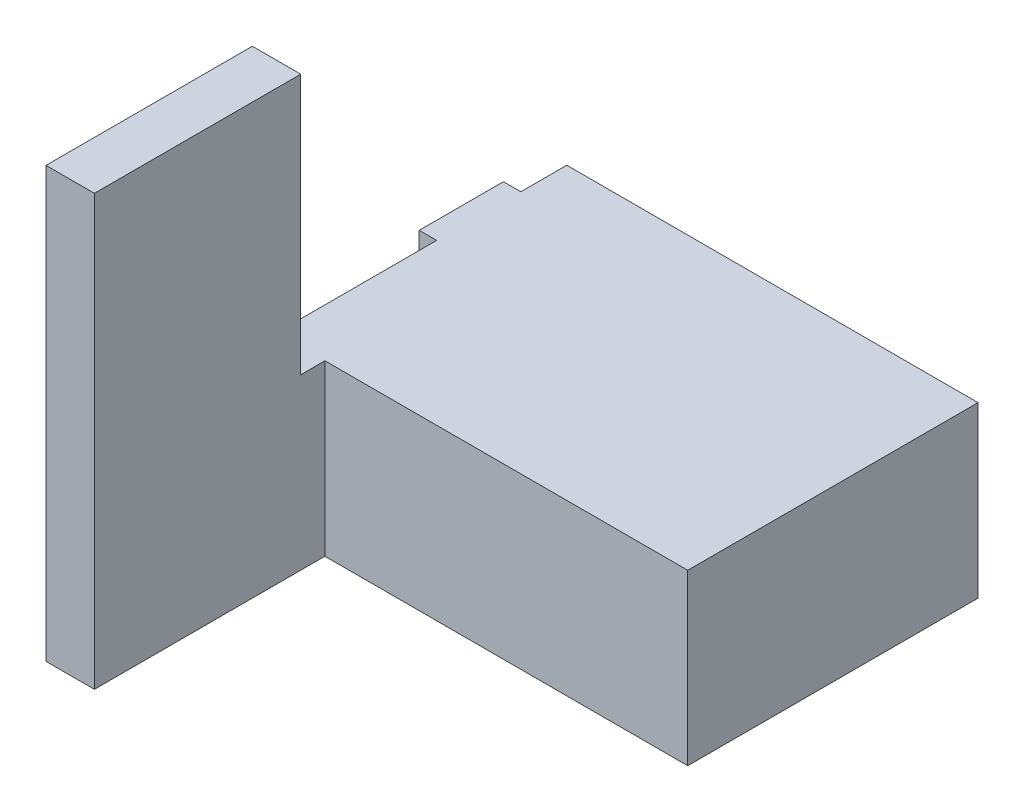
SolidWorks part; units mm, degrees
ref_plane "Front Plane" through (0, 0, 0) normal (0, 0, 1) x (1, 0, 0)
ref_plane "Top Plane" through (0, 0, 0) normal (0, 1, 0) x (1, 0, 0)
ref_plane "Right Plane" through (0, 0, 0) normal (1, 0, 0) x (0, 0, -1)
sketch "Sketch1" plane through (0, 0, 0) normal (0, 1, 0) x (1, 0, 0)
  line L1 (-82.55, 86.0758) -> (107.95, 86.0758)
  line L3 (-82.55, -66.3242) -> (107.95, -66.3242)
  line L4 (107.95, 86.0758) -> (107.95, -66.3242)
  line L9 (-82.55, 86.0758) -> (-107.95, 86.0758)
  line L10 (-82.55, -66.3242) -> (-82.55, -187.3552)
  line L11 (-82.55, -187.3552) -> (-107.95, -187.3552)
  line L12 (-107.95, 86.0758) -> (-107.95, -187.3552)
  dimension "D1" = 190.5
  dimension "D2" = 152.4
  dimension "D5" = 25.4
  dimension "D6" = 273.431
extrude "Boss-Extrude2" add sketch "Sketch1" along normal blind 88.9
sketch "Sketch2" plane through (0, 88.9, 0) normal (0, 1, 0) x (1, 0, 0)
  line L0 (-107.95, 86.0758) -> (-107.95, -187.3552) construction
  line L1 (-107.95, -79.0242) -> (-82.55, -79.0242)
  line L2 (-107.95, -79.0242) -> (-107.95, -187.3552)
  line L3 (-107.95, -187.3552) -> (-82.55, -187.3552)
  line L4 (-82.55, -79.0242) -> (-82.55, -187.3552)
  line L5 (-82.55, -66.3242) -> (107.95, -66.3242) construction
  dimension "D1" = 12.7
extrude "Boss-Extrude3" add sketch "Sketch2" along normal blind 136.652
hole_wizard "M4x0.7 Tapped Hole2" positions "3DSketch1" profile "Sketch4" tap size "M4x0.7" standard "ANSI Metric"
sketch3d "3DSketch1"
  line L0 (107.95, 0, -86.0758) -> (-107.95, 0, -86.0758) construction
  line L1 (107.95, 0, 66.3242) -> (107.95, 0, -86.0758) construction
  line L2 (-107.95, 0, -86.0758) -> (-107.95, 0, 187.3552) construction
  line L3 (-82.55, 0, 66.3242) -> (107.95, 0, 66.3242) construction
  line L4 (-107.95, 0, 187.3552) -> (-82.55, 0, 187.3552) construction
  point P0 (95.25, 0, -73.3758)
  point P2 (-96.774, 0, -73.3758)
  point P4 (46.99, 0, 53.6242)
  point P6 (-96.774, 0, 174.6552)
  point P20 (-96.774, 0, 91.7242)
  dimension "D1" = 12.7
  dimension "D2" = 12.7
  dimension "D3" = 11.176
  dimension "D4" = 12.7
  dimension "D5" = 60.96
  dimension "D6" = 12.7
  dimension "D7" = 11.176
  dimension "D8" = 12.7
  dimension "D9" = 11.176
  dimension "D10" = 165.1
sketch "Sketch4" plane through (95.25, 0, -73.3758) normal (1, 0, 0) x (0, 0, -1)
  line L0 (0, 0) -> (0, 10.8974)
  line L1 (0, 10.8974) -> (1.65, 9.906)
  line L2 (1.65, 9.906) -> (1.65, 0)
  line L5 (1.65, 0) -> (0, 0)
  line L10 (0, 10.8974) -> (-1.65, 9.906) construction
  line L11 (0, -6.35) -> (0, 107.95) construction
  dimension "Tap Drill Dia." = 3.3
  dimension "Tap Drill Depth" = 9.906
  dimension "Drill Angle" = 118
cosmetic thread "Hole Thread5" parameters "D1"=7.874, "D2"=4
cosmetic thread "Hole Thread6" parameters "D1"=7.874, "D2"=4
cosmetic thread "Hole Thread7" parameters "D1"=7.874, "D2"=4
cosmetic thread "Hole Thread8" parameters "D1"=7.874, "D2"=4
cosmetic thread "Hole Thread9" parameters "D1"=7.874, "D2"=4
sketch "Sketch5" plane through (-107.95, 0, 0) normal (-1, 0, 0) x (0, 0, 1)
  line L0 (-86.0758, 88.9) -> (79.0242, 88.9) construction
  line L1 (-61.9458, 88.9) -> (-17.7498, 88.9)
  line L2 (-61.9458, 88.9) -> (-61.9458, 44.704)
  line L3 (-61.9458, 44.704) -> (-17.7498, 44.704)
  line L4 (-17.7498, 88.9) -> (-17.7498, 44.704)
  line L5 (-86.0758, 88.9) -> (-86.0758, 0) construction
  dimension "D1" = 24.13
  dimension "D2" = 44.196
  dimension "D3" = 44.196
extrude "Boss-Extrude4" add sketch "Sketch5" along normal blind 9.144
